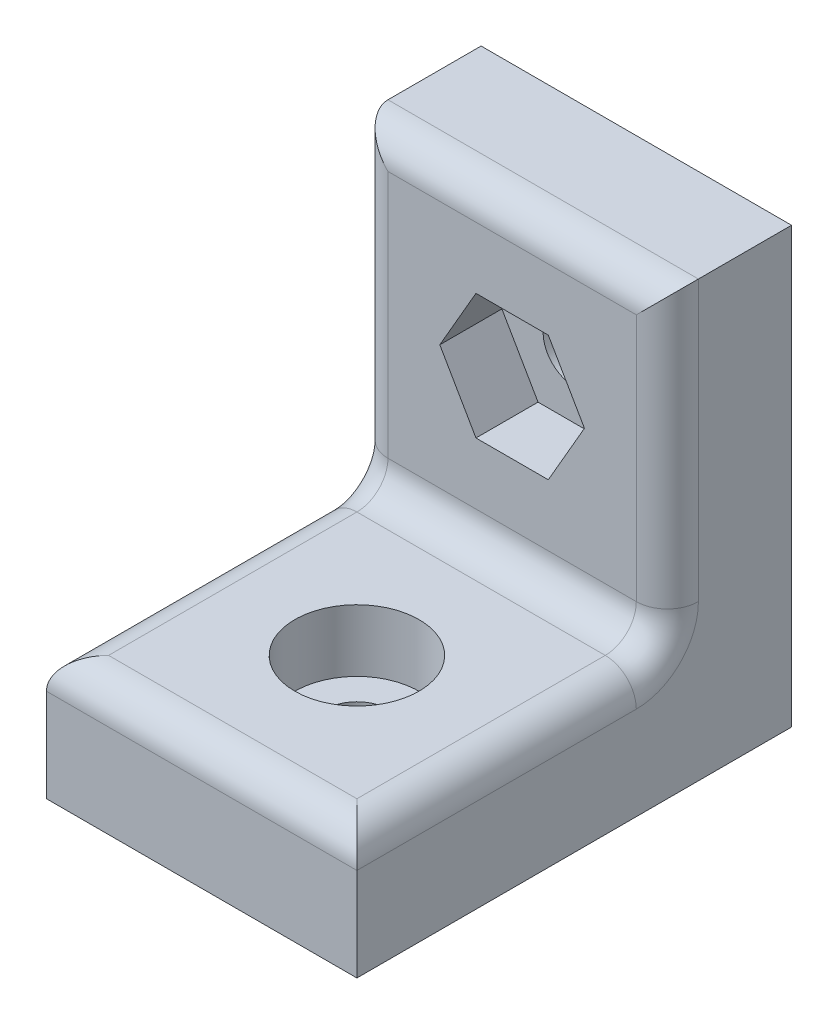
SolidWorks part; units mm, degrees
ref_plane "Plan de face" through (0, 0, 0) normal (0, 0, 1) x (1, 0, 0)
ref_plane "Plan de dessus" through (0, 0, 0) normal (0, 1, 0) x (1, 0, 0)
ref_plane "Plan de droite" through (0, 0, 0) normal (1, 0, 0) x (0, 0, -1)
sketch "Esquisse1" plane through (0, 0, 0) normal (0, 0, 1) x (1, 0, 0)
  line L1 (-5, 14) -> (5, 14)
  line L2 (-5, 14) -> (-5, 0)
  line L3 (-5, 0) -> (5, 0)
  line L4 (5, 14) -> (5, 0)
  dimension "D1" = 10
  dimension "D2" = 14
  dimension "D3" = 5
extrude "Boss.-Extru.1" add sketch "Esquisse1" along normal blind 4
sketch "Esquisse2" plane through (0, 0, 4) normal (0, 0, 1) x (1, 0, 0)
  line L0 (5, 0) -> (5, 14) construction
  line L1 (-5, 0) -> (5, 0)
  line L2 (-5, 0) -> (-5, 4)
  line L3 (-5, 4) -> (5, 4)
  line L4 (5, 0) -> (5, 4)
  dimension "D1" = 4
extrude "Boss.-Extru.2" add sketch "Esquisse2" along normal blind 10
sketch "Esquisse3" plane through (0, 0, 4) normal (0, 0, 1) x (1, 0, 0)
  line L0 (5, 14) -> (-5, 14) construction
  line L1 (-5, 14) -> (-5, 4) construction
  circle A0 centre (0, 9) radius 1
  point P2 (0, 14)
  point P3 (-5, 9)
  dimension "D1" = 2
extrude "Enlèv. mat.-Extru.1" cut sketch "Esquisse3" against normal through all
fillet "Congé1" radius 1 7 edges at (0, 4, 4) (5, 9, 4) (-5, 9, 4) (0, 14, 4) (0, 4, 14) (5, 4, 9) (-5, 4, 9)
sketch "Esquisse4" plane through (0, 4, 0) normal (0, 1, 0) x (1, 0, 0)
  line L0 (5, -14) -> (-5, -14) construction
  line L1 (-5, -14) -> (-5, -4) construction
  circle A0 centre (0, -9) radius 1
  point P0 (0, -14)
  point P1 (-5, -9)
  dimension "D1" = 2
extrude "Enlèv. mat.-Extru.2" cut sketch "Esquisse4" against normal through all
sketch "Esquisse5" plane through (0, 0, 4) normal (0, 0, 1) x (1, 0, 0)
  line L0 (5, 14) -> (-5, 14) construction
  line L1 (1.165, 6.9822) -> (2.33, 9)
  line L2 (2.33, 9) -> (1.165, 11.0178)
  line L3 (1.165, 11.0178) -> (-1.165, 11.0178)
  line L4 (-1.165, 11.0178) -> (-2.33, 9)
  line L5 (-2.33, 9) -> (-1.165, 6.9822)
  line L6 (-1.165, 6.9822) -> (1.165, 6.9822)
  circle A1 centre (0, 9) radius 2.0178 construction
  dimension "D1" = 2.33
extrude "Enlèv. mat.-Extru.3" cut sketch "Esquisse5" against normal blind 2
sketch "Esquisse6" plane through (0, 4, 0) normal (0, 1, 0) x (1, 0, 0)
  circle A0 centre (0, -9) radius 2
  dimension "D1" = 4
extrude "Enlèv. mat.-Extru.4" cut sketch "Esquisse6" against normal blind 2
